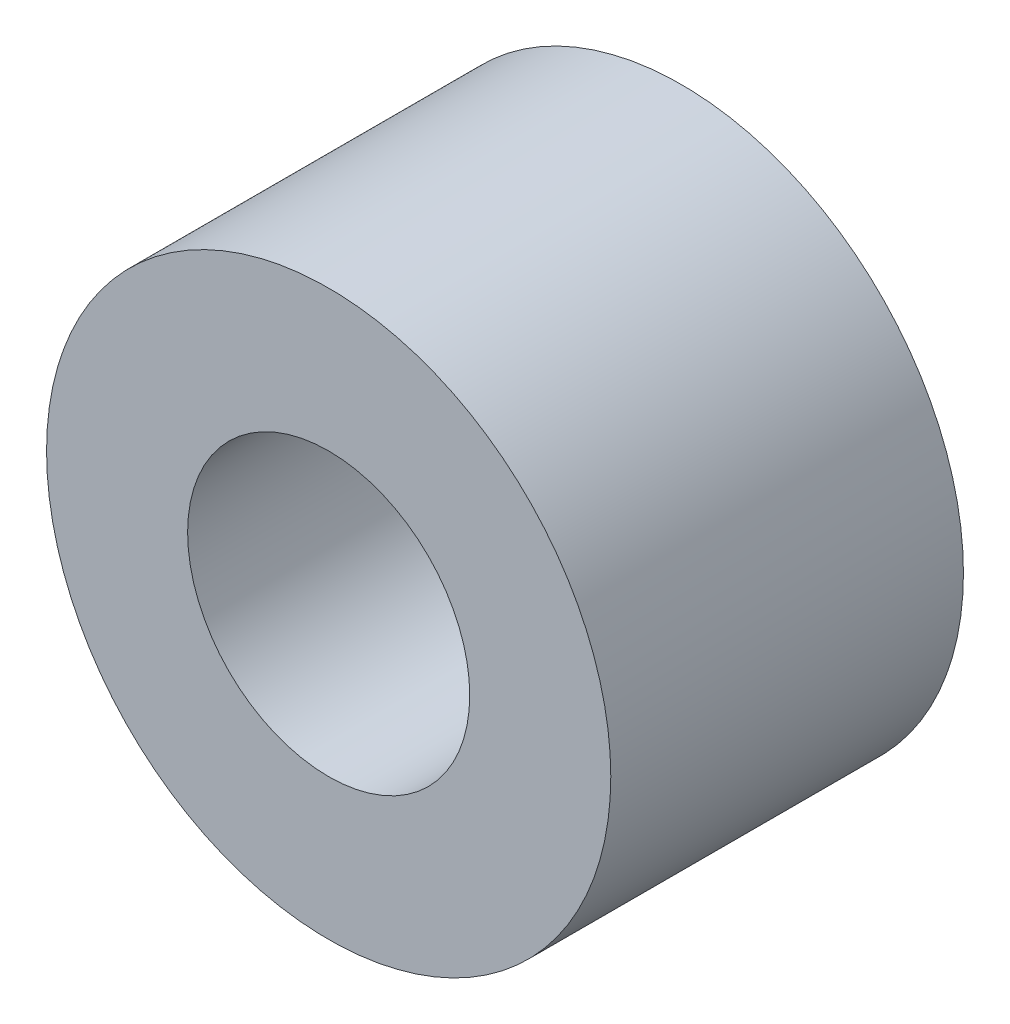
SolidWorks part; units mm, degrees
ref_plane "Front Plane" through (0, 0, 0) normal (0, 0, 1) x (1, 0, 0)
ref_plane "Top Plane" through (0, 0, 0) normal (0, 1, 0) x (1, 0, 0)
ref_plane "Right Plane" through (0, 0, 0) normal (1, 0, 0) x (0, 0, -1)
sketch "Sketch1" plane through (0, 0, 0) normal (0, 0, 1) x (1, 0, 0)
  circle A0 centre (2.3449, 1.2481) radius 4
  circle A1 centre (2.3449, 1.2481) radius 2
  dimension "4" = 4
  dimension "D2" = 8
extrude "Boss-Extrude1" add sketch "Sketch1" along normal blind 5
